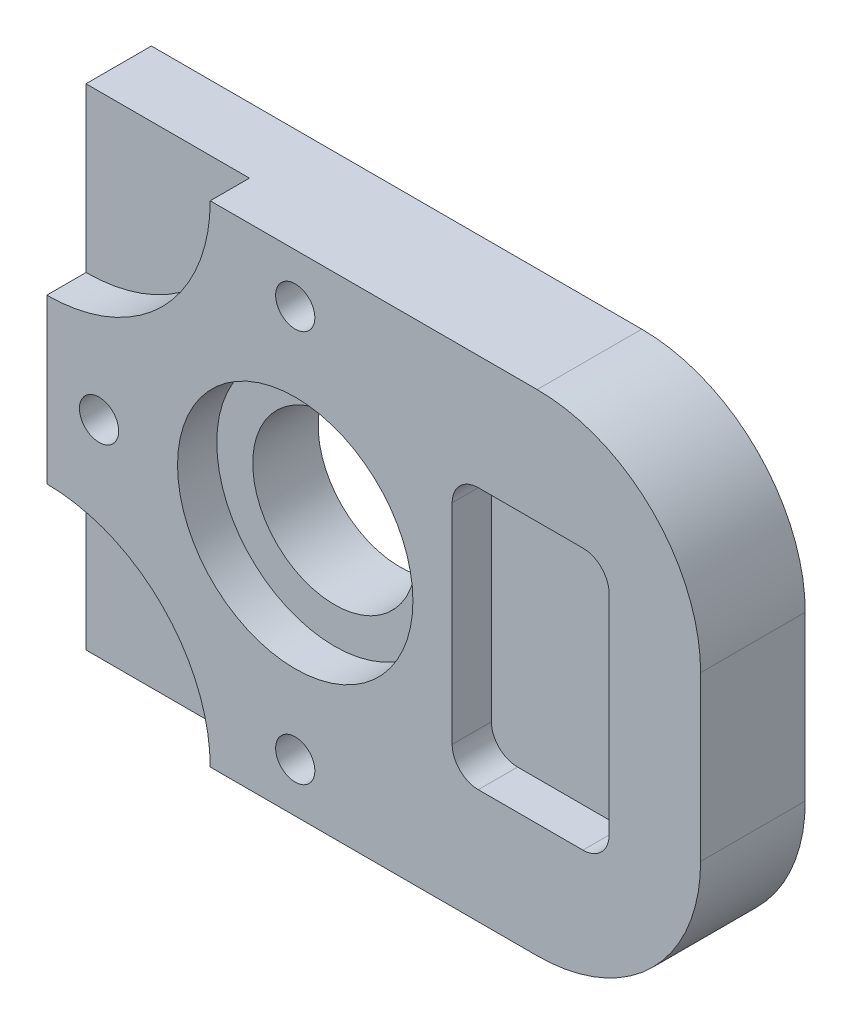
SolidWorks part; units mm, degrees
ref_plane "Front" through (0, 0, 0) normal (0, 0, 1) x (1, 0, 0)
ref_plane "Top" through (0, 0, 0) normal (0, 1, 0) x (1, 0, 0)
ref_plane "Right" through (0, 0, 0) normal (1, 0, 0) x (0, 0, -1)
sketch "Sketch1" plane through (0, 0, 0) normal (0, 0, 1) x (1, 0, 0)
  line L1 (0, 75) -> (75, 75)
  line L2 (0, 75) -> (0, 0)
  line L3 (0, 0) -> (75, 0)
  line L4 (100, 50) -> (100, 25)
  arc A0 (75, 75) -> (100, 50) centre (75, 50) cw
  arc A1 (75, 0) -> (100, 25) centre (75, 25) ccw
  dimension "D3" = 25
  dimension "D1" = 100
  dimension "D2" = 75
extrude "Extrude1" add sketch "Sketch1" along normal blind 16
sketch "Sketch2" plane through (0, 0, 16) normal (0, 0, 1) x (1, 0, 0)
  line L0 (0, 75) -> (0, 0) construction
  line L1 (0, 37.5) -> (119.9341, 37.5) construction
  circle A0 centre (38, 37.5) radius 12.5
  dimension "D1" = 25
  dimension "D2" = 38
extrude "Cut-Extrude1" cut sketch "Sketch2" against normal through all
sketch "Sketch3" plane through (0, 0, 16) normal (0, 0, 1) x (1, 0, 0)
  circle A0 centre (38, 37.5) radius 18
  dimension "D1" = 36
extrude "Cut-Extrude2" cut sketch "Sketch3" against normal blind 6
sketch "Sketch4" plane through (0, 0, 16) normal (0, 0, 1) x (1, 0, 0)
  line L0 (0, 75) -> (0, 0) construction
  line L1 (62, 57.5) -> (86, 57.5)
  line L2 (62, 57.5) -> (62, 17.5)
  line L3 (62, 17.5) -> (86, 17.5)
  line L4 (86, 57.5) -> (86, 17.5)
  line L5 (0, 37.5) -> (109.0255, 37.5) construction
  dimension "D1" = 62
  dimension "D2" = 24
  dimension "D3" = 40
extrude "Cut-Extrude3" cut sketch "Sketch4" against normal blind 6
fillet "Fillet1" radius 4 4 edges at (62, 17.5, 13) (86, 17.5, 13) (86, 57.5, 13) (62, 57.5, 13)
hole_wizard "Hole1" positions "Sketch6" profile "Sketch5" legacy end condition through all
sketch "Sketch6" plane through (0, 0, 16) normal (0, 0, 1) x (1, 0, 0)
  line L0 (0, 75) -> (0, 0) construction
  line L1 (0, 37.5) -> (23.1622, 37.5) construction
  line L2 (38, 37.5) -> (38, 88.0413) construction
  point P0 (38, 67.5)
  point P1 (8, 37.5)
  point P3 (38, 7.5)
  dimension "D1" = 8
  dimension "D2" = 60
sketch "Sketch5" plane through (38, 67.5, 16) normal (1, 0, 0) x (0, -1, 0)
  line L0 (0, 0) -> (0, 16)
  line L1 (0, 16) -> (3, 16)
  line L2 (3, 16) -> (3, 0)
  line L3 (3, 0) -> (0, 0)
  line L4 (0, 110) -> (0, -10) construction
  dimension "Diameter" = 6
  dimension "Depth" = 16
sketch "Sketch7" plane through (0, 0, 16) normal (0, 0, 1) x (1, 0, 0)
  circle A0 centre (0, 75) radius 25
  circle A1 centre (0, 0) radius 25
  dimension "D1" = 50
extrude "Cut-Extrude4" cut sketch "Sketch7" against normal blind 6
